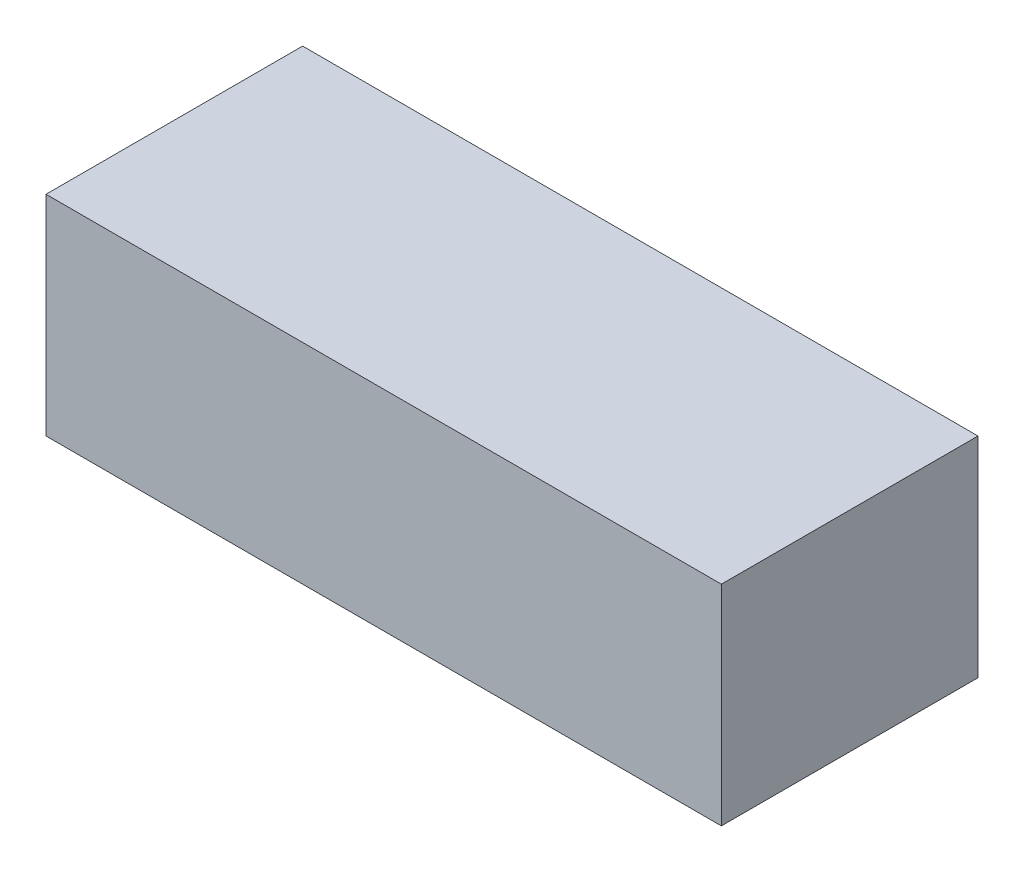
SolidWorks part; units mm, degrees
ref_plane "Front Plane" through (0, 0, 0) normal (0, 0, 1) x (1, 0, 0)
ref_plane "Top Plane" through (0, 0, 0) normal (0, 1, 0) x (1, 0, 0)
ref_plane "Right Plane" through (0, 0, 0) normal (1, 0, 0) x (0, 0, -1)
sketch "Sketch1" plane through (0, 0, 0) normal (0, 1, 0) x (1, 0, 0)
  line L1 (0, 0) -> (200, 0)
  line L2 (0, 0) -> (0, 76)
  line L3 (0, 76) -> (200, 76)
  line L4 (200, 0) -> (200, 76)
  line L5 (0, 0) -> (200, 76) construction
  line L6 (0, 76) -> (200, 0) construction
  point P4 (100, 38)
  dimension "D1" = 76
  dimension "D2" = 200
extrude "Boss-Extrude1" add sketch "Sketch1" along normal blind 62
